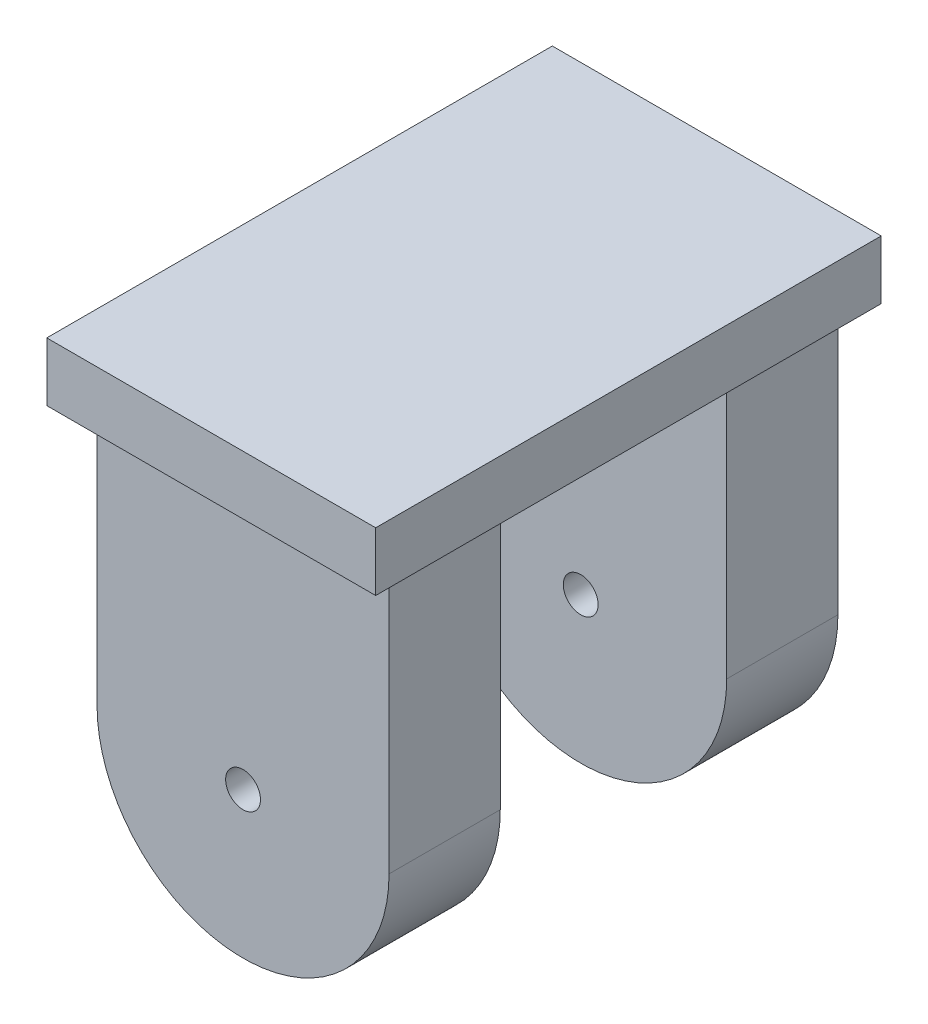
SolidWorks part; units mm, degrees
ref_plane "Front Plane" through (0, 0, 0) normal (0, 0, 1) x (1, 0, 0)
ref_plane "Top Plane" through (0, 0, 0) normal (0, 1, 0) x (1, 0, 0)
ref_plane "Right Plane" through (0, 0, 0) normal (1, 0, 0) x (0, 0, -1)
sketch "Sketch4" plane through (0, 0, 0) normal (0, 0, 1) x (1, 0, 0)
  line L0 (-21.4924, 31.4285) -> (-21.4924, 107.442)
  line L1 (-21.4924, 107.442) -> (62.3337, 107.442)
  line L2 (62.3337, 31.4285) -> (62.3337, 107.442)
  arc A0 (-21.4924, 31.4285) -> (62.3337, 31.4285) centre (20.4206, 31.4285) ccw
  circle A1 centre (20.4206, 31.4285) radius 5
extrude "Boss-Extrude4" add sketch "Sketch4" along normal mid plane 128.8447
sketch "Sketch6" plane through (0, 107.442, 0) normal (0, 1, 0) x (1, 0, 0)
  line L6 (-27.179, -73.1629) -> (67.2333, -73.1629)
  line L7 (-27.179, -73.1629) -> (-27.179, 71.9533)
  line L8 (-27.179, 71.9533) -> (67.2333, 71.9533)
  line L9 (67.2333, -73.1629) -> (67.2333, 71.9533)
extrude "Boss-Extrude5" add sketch "Sketch6" along normal blind 16.8447
sketch "Sketch7" plane through (0, 0, 0) normal (0, 0, 1) x (1, 0, 0)
  line L1 (-32.3568, 107.442) -> (72.9568, 107.442)
  line L2 (-32.3568, 107.442) -> (-32.3568, -20.0378)
  line L3 (-32.3568, -20.0378) -> (72.9568, -20.0378)
  line L4 (72.9568, 107.442) -> (72.9568, -20.0378)
extrude "Cut-Extrude1" cut sketch "Sketch7" against normal mid plane 65
